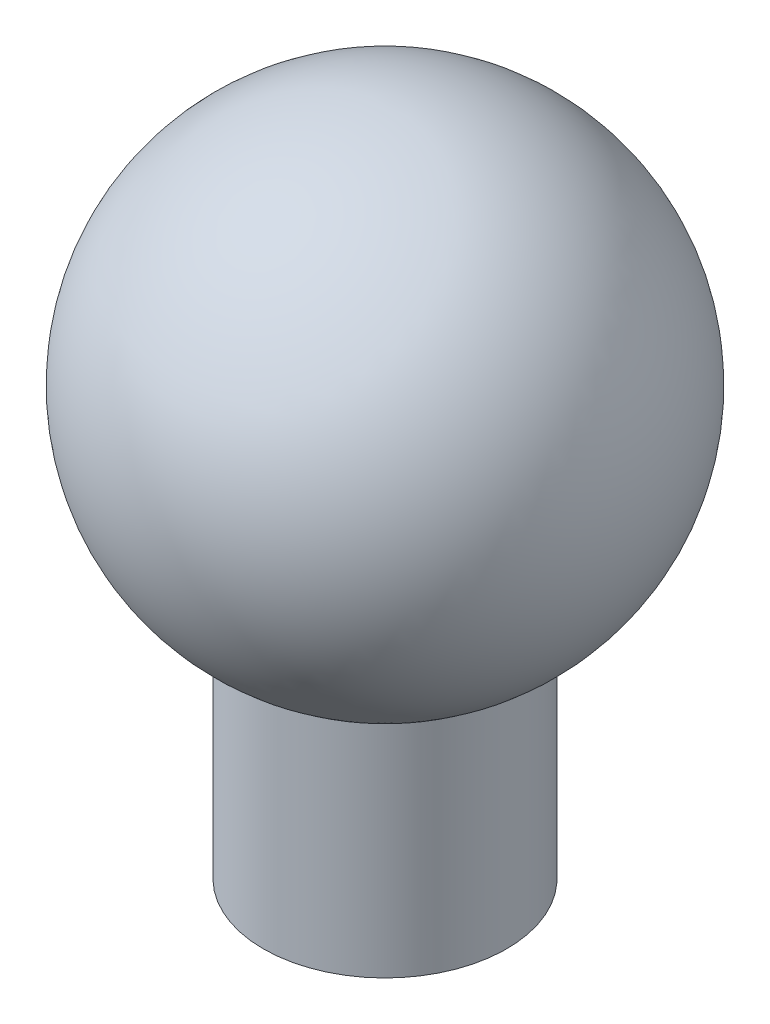
SolidWorks part; units mm, degrees
ref_plane "Front" through (0, 0, 0) normal (0, 0, 1) x (1, 0, 0)
ref_plane "Top" through (0, 0, 0) normal (0, 1, 0) x (1, 0, 0)
ref_plane "Right" through (0, 0, 0) normal (1, 0, 0) x (0, 0, -1)
sketch "Sketch1" plane through (0, 0, 0) normal (0, 1, 0) x (1, 0, 0)
  circle A0 centre (0, 0) radius 4.191
  dimension "D1" = 8.382
extrude "Base-Extrude" add sketch "Sketch1" along normal blind 7.62
sketch "Sketch2" plane through (0, 0, 0) normal (0, 0, 1) x (1, 0, 0)
  line L0 (0, 0) -> (0, 14.986) construction
  line L1 (0, 7.62) -> (0, 0) construction
  line L2 (-4.191, 0) -> (4.191, 0) construction
  line L4 (0, 22.987) -> (0, 6.477)
  arc A0 (0, 6.477) -> (0, 22.987) centre (0, 14.732) ccw
  dimension "D1" = 14.732
  dimension "D2" = 16.51
revolve "Boss-Revolve1" add sketch "Sketch2" angle 360 about L0
scale "Scale1" scale about centroid uniform scaling yes scale factor 5.55
